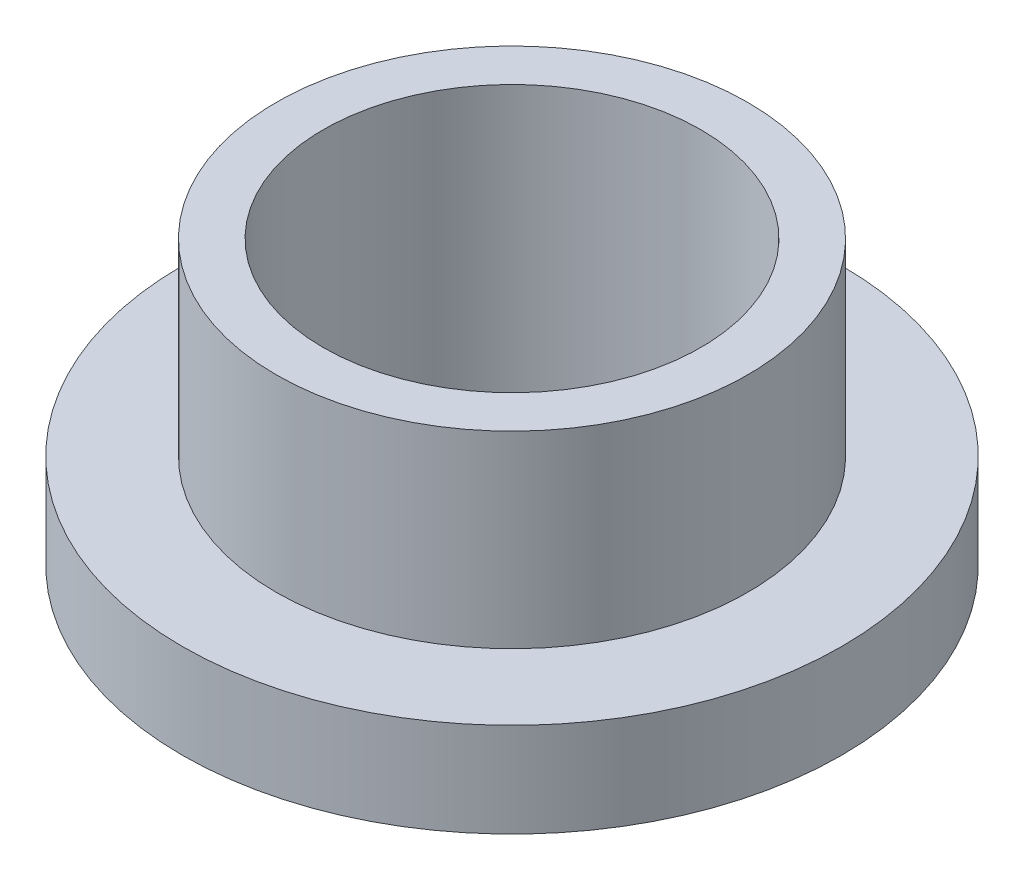
SolidWorks part; units mm, degrees
ref_plane "Front" through (0, 0, 0) normal (0, 0, 1) x (1, 0, 0)
ref_plane "Top" through (0, 0, 0) normal (0, 1, 0) x (1, 0, 0)
ref_plane "Right" through (0, 0, 0) normal (1, 0, 0) x (0, 0, -1)
sketch "Sketch1" plane through (0, 0, 0) normal (0, 1, 0) x (1, 0, 0)
  circle A0 centre (0, 0) radius 6.3627
  circle A1 centre (0, 0) radius 7.9502
  circle A2 centre (0, 0) radius 11.1125
  dimension "ID" = 12.7254
  dimension "OD" = 15.9004
  dimension "FlangeOD" = 22.225
sketch "Sketch2" plane through (0, 0, 0) normal (0, 1, 0) x (1, 0, 0)
  circle A0 centre (0, 0) radius 6.3627 construction
  circle A1 centre (0, 0) radius 7.9502 construction
  circle A2 centre (0, 0) radius 6.3627
  circle A3 centre (0, 0) radius 7.9502
extrude "Boss-Extrude1" add sketch "Sketch2" along normal blind 9.525
sketch "Sketch3" plane through (0, 0, 0) normal (0, 1, 0) x (1, 0, 0)
  circle A0 centre (0, 0) radius 11.1125 construction
  circle A1 centre (0, 0) radius 7.9502 construction
  circle A2 centre (0, 0) radius 11.1125
  circle A3 centre (0, 0) radius 7.9502
extrude "Boss-Extrude2" add sketch "Sketch3" along normal blind 3.175
